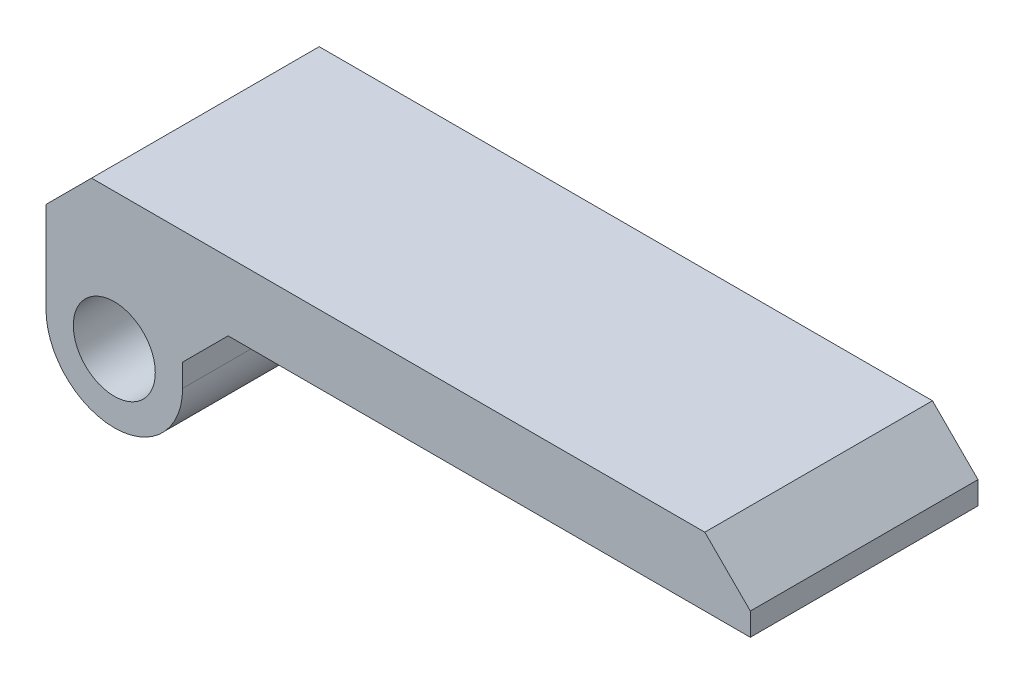
SolidWorks part; units mm, degrees
ref_plane "Front Plane" through (0, 0, 0) normal (0, 0, 1) x (1, 0, 0)
ref_plane "Top Plane" through (0, 0, 0) normal (0, 1, 0) x (1, 0, 0)
ref_plane "Right Plane" through (0, 0, 0) normal (1, 0, 0) x (0, 0, -1)
sketch "Sketch1" plane through (0, 0, 0) normal (0, 0, 1) x (1, 0, 0)
  line L1 (0, 0) -> (120, 0)
  line L2 (0, 0) -> (0, 60)
  line L3 (0, 60) -> (120, 60)
  line L4 (120, 0) -> (120, 60)
  dimension "D1" = 120
  dimension "D2" = 60
extrude "Boss-Extrude1" add sketch "Sketch1" along normal blind 2
chamfer "Chamfer2" distance 10 angle 45 4 edges at (120, 0, 1) (0, 0, 1) (0, 60, 1) (120, 60, 1)
sketch "Sketch2" plane through (0, 0, 2) normal (0, 0, 1) x (1, 0, 0)
  line L0 (10.8284, 2) -> (109.1716, 2)
  line L1 (109.1716, 2) -> (118, 10.8284)
  line L2 (118, 10.8284) -> (118, 49.1716)
  line L3 (118, 49.1716) -> (109.1716, 58)
  line L4 (79.1716, 58) -> (40.8284, 58)
  line L5 (10.8284, 58) -> (2, 49.1716)
  line L6 (2, 49.1716) -> (2, 10.8284)
  line L7 (2, 10.8284) -> (10.8284, 2)
  line L8 (10, 0) -> (110, 0)
  line L9 (110, 0) -> (120, 10)
  line L10 (120, 10) -> (120, 50)
  line L11 (120, 50) -> (110, 60)
  line L12 (110, 60) -> (10, 60)
  line L13 (10, 60) -> (0, 50)
  line L14 (0, 50) -> (0, 10)
  line L15 (0, 10) -> (10, 0)
  line L16 (10, 0) -> (110, 0)
  line L17 (110, 0) -> (120, 10)
  line L18 (120, 10) -> (120, 50)
  line L19 (120, 50) -> (110, 60)
  line L20 (110, 60) -> (109.1716, 60)
  line L21 (10, 60) -> (0, 50)
  line L22 (0, 50) -> (0, 10)
  line L23 (0, 10) -> (10, 0)
  line L24 (10.8284, 60) -> (10, 60)
  line L26 (10.8284, 58) -> (10.8284, 60)
  line L28 (40.8284, 58) -> (40.8284, 60)
  line L30 (109.1716, 58) -> (109.1716, 60)
  line L32 (79.1716, 58) -> (79.1716, 60)
  line L33 (110, 60) -> (10, 60) construction
  line L34 (109.1716, 58) -> (10.8284, 58) construction
  line L35 (79.1716, 60) -> (40.8284, 60)
  dimension "D3" = 30
  dimension "D4" = 30
  dimension "D1" = 0
  dimension "D2" = 2
extrude "Boss-Extrude2" add sketch "Sketch2" along normal blind 15
fillet "Fillet1" radius 2 8 edges at (60, 2, 2) (6.4142, 6.4142, 2) (2, 30, 2) (6.4142, 53.5858, 2) (113.5858, 6.4142, 2) (118, 30, 2) (113.5858, 53.5858, 2) (60, 58, 2)
sketch "Sketch4" plane through (0, 0, 2) normal (0, 0, 1) x (1, 0, 0)
  line L0 (40.8284, 58) -> (79.1716, 58) construction
  line L1 (79.1716, 60) -> (40.8284, 60) construction
  circle A0 centre (33, 41) radius 1
  circle A1 centre (33, 41) radius 2.5
  point P7 (60, 60)
  dimension "D1" = 2
  dimension "D2" = 5
  dimension "D3" = 17
  dimension "D4" = 27
extrude "Boss-Extrude3" add sketch "Sketch4" along normal blind 4
sketch "Sketch6" plane through (0, 0, 2) normal (0, 0, 1) x (1, 0, 0)
  line L0 (10, 0) -> (110, 0) construction
  line L1 (29.5, 16.6) -> (90.5, 16.6)
  line L2 (29.5, 16.6) -> (29.5, 2)
  line L3 (29.5, 2) -> (90.5, 2)
  line L4 (90.5, 16.6) -> (90.5, 2)
  line L5 (109.1716, 2) -> (10.8284, 2) construction
  point P6 (60, 2)
  point P10 (60, 0)
  dimension "D1" = 61
  dimension "D2" = 14.6
extrude "Boss-Extrude5" add sketch "Sketch6" along normal up to surface (15 mm away) contours L2 L1 L4 L3 up to face at (60, 33.3333, 17)
sketch "Sketch7" plane through (29.5, 0, 0) normal (-1, 0, 0) x (0, 0, 1)
  line L0 (17, 16.6) -> (2, 16.6) construction
  line L1 (9.5, 16.6) -> (20.8532, 16.6)
  line L2 (9.5, 16.6) -> (9.5, 2)
  line L3 (9.5, 2) -> (20.8532, 2)
  line L4 (20.8532, 16.6) -> (20.8532, 2)
  line L5 (17, 2) -> (4, 2) construction
  circle A0 centre (9.5, 9.3) radius 7.3
  line M8 (4, 2) -> (17, 2)
  line M9 (17, 2) -> (17, 16.6)
  line M10 (17, 16.6) -> (2, 16.6)
extrude "Cut-Extrude2" cut sketch "Sketch7" against normal blind 55 from offset 3 contours L2 A0 | L2 A0 | A0 M8 M9 M10 offset against normal yes
chamfer "Chamfer3" distance 4 angle 45 2 edges at (31, 16.6, 17) (89, 16.6, 17)
sketch "Sketch9" plane through (0, 0, 2) normal (0, 0, 1) x (1, 0, 0)
  line L0 (38, 49) -> (52, 49)
  line L1 (40, 47) -> (50, 47)
  line L2 (40, 47) -> (40, 35)
  line L3 (40, 35) -> (50, 35)
  line L4 (50, 47) -> (50, 35)
  line L5 (52, 49) -> (52, 33)
  line L6 (38, 33) -> (52, 33)
  line L7 (38, 49) -> (38, 33)
  point P9 (33, 41)
  point P10 (38, 41)
  dimension "D1" = 10
  dimension "D2" = 12
  dimension "D4" = 5
  dimension "D3" = 2
extrude "Boss-Extrude6" add sketch "Sketch9" along normal up to surface (4 mm away) up to face at (35.5, 41, 6)
sketch "Sketch10" plane through (0, 0, 2) normal (0, 0, 1) x (1, 0, 0)
  line L0 (40.8284, 60) -> (10.8284, 60) construction
  line L2 (60, 60) -> (60, 72.9094) construction
  line L3 (79.1716, 60) -> (40.8284, 60) construction
  line L4 (10.8284, 55.1716) -> (10.8284, 60) construction
  circle A0 centre (14.8284, 57) radius 1.5
  circle A1 centre (14.8284, 57) radius 3
  circle A2 centre (105.1716, 57) radius 3
  circle A3 centre (105.1716, 57) radius 1.5
  dimension "D1" = 3
  dimension "D2" = 6
  dimension "D3" = 4
extrude "Boss-Extrude8" add sketch "Sketch10" along normal blind 4
sketch "Sketch12" plane through (0, 0, 17) normal (0, 0, 1) x (1, 0, 0)
  line L0 (11.8284, 57) -> (11.8284, 63)
  line L1 (11.8284, 63) -> (42.7658, 63)
  line L2 (42.7658, 63) -> (42.7658, 60)
  line L3 (42.7658, 60) -> (17.8284, 60)
  line L4 (17.8284, 60) -> (17.8284, 57)
  line L5 (79.1716, 60) -> (40.8284, 60) construction
  line L6 (10.8284, 58) -> (10.8284, 60) construction
  circle A0 centre (14.8284, 57) radius 1.8
  circle A1 centre (14.8284, 57) radius 3
  point P4 (11.8284, 57)
  dimension "D1" = 3.6
  dimension "D2" = 6
  dimension "D3" = 3
  dimension "D4" = 1
extrude "Boss-Extrude9" add sketch "Sketch12" along normal blind 10 from offset 10 separate body contours A1 A0 | A1 L4 L3 L2 L1 L0
chamfer "Chamfer4" distance 2 angle 45 3 edges at (42.7658, 63, 32) (17.8284, 60, 32) (11.8284, 63, 32)
sketch "Sketch13" plane through (0, 60, 0) normal (0, 1, 0) x (1, 0, 0)
  line L1 (-10.7992, 11.4461) -> (131.5646, 11.4461)
  line L2 (-10.7992, 11.4461) -> (-10.7992, -25.1015)
  line L3 (-10.7992, -25.1015) -> (131.5646, -25.1015)
  line L4 (131.5646, 11.4461) -> (131.5646, -25.1015)
extrude "Cut-Extrude3" cut sketch "Sketch13" against normal blind 85
sketch "Sketch14" plane through (0, 0, 37) normal (0, 0, 1) x (1, 0, 0)
  line L0 (32.8284, 60) -> (32.8284, 61.5)
  line L1 (42.7658, 60) -> (19.8284, 60) construction
  line L2 (32.8284, 61.5) -> (17.8284, 61.5)
  line L3 (17.8284, 61.5) -> (17.8284, 58)
  line L4 (17.8284, 58) -> (28.9112, 56.8575)
  line L5 (28.9112, 56.8575) -> (32.8284, 60)
  line L6 (11.8284, 57) -> (11.8284, 61) construction
  dimension "D1" = 1.5
  dimension "D2" = 15
extrude "Cut-Extrude4" cut sketch "Sketch14" against normal blind 2 from offset 4
